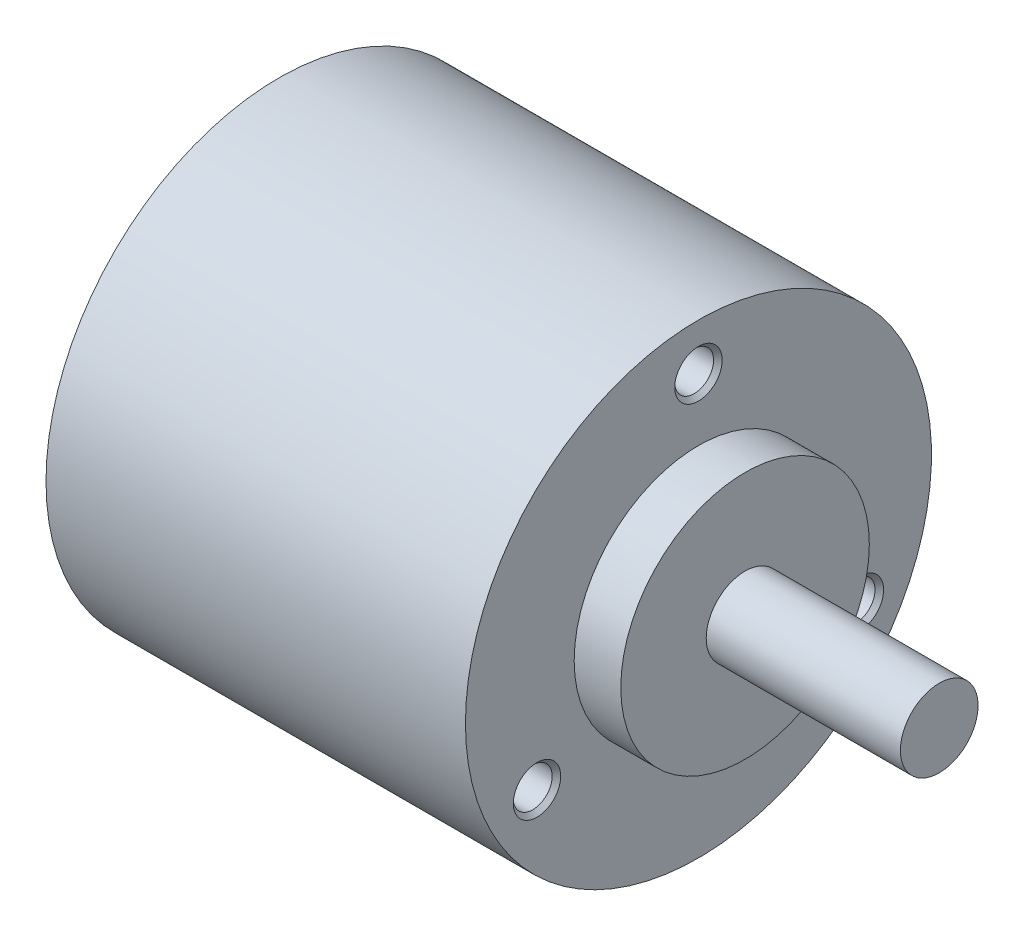
SolidWorks part; units mm, degrees
ref_plane "Plan de face" through (0, 0, 0) normal (0, 0, 1) x (1, 0, 0)
ref_plane "Plan de dessus" through (0, 0, 0) normal (0, 1, 0) x (1, 0, 0)
ref_plane "Plan de droite" through (0, 0, 0) normal (1, 0, 0) x (0, 0, -1)
sketch "Esquisse1" plane through (0, 0, 0) normal (0, 0, 1) x (1, 0, 0)
  line L0 (-51.1551, 0) -> (25.063, 0) construction
  line L1 (15.5, 2.5) -> (15.5, 0)
  line L2 (15.5, 0) -> (-27, 0)
  line L3 (-27, 0) -> (-27, 15)
  line L4 (-27, 15) -> (0, 15)
  line L5 (0, 15) -> (0, 8)
  line L6 (3, 2.5) -> (15.5, 2.5)
  line L7 (0, 8) -> (3, 8)
  line L8 (3, 8) -> (3, 2.5)
  dimension "D1" = 30
  dimension "D2" = 5
  dimension "D3" = 15.5
  dimension "D4" = 27
  dimension "D5" = 3
  dimension "D6" = 16
revolve "Révolution1" add sketch "Esquisse1" angle 360 about L0
hole_wizard "Trou taraudé M3x0.51" positions "Esquisse4" profile "Esquisse3" tap size "M3x0.5" standard "Ansi Metric"
sketch "Esquisse4" plane through (0, 0, 0) normal (1, 0, 0) x (0, 0, -1)
  circle A0 centre (0, 0) radius 12 construction
  point P0 (0, 12)
  point P2 (-10.3923, -6)
  point P8 (10.3923, -6)
  point P11 (0, 0)
  point P12 (0, -11)
  point P13 (-8.3544, -7.1557)
  dimension "D1" = 24
  dimension "D2" = 120
sketch "Esquisse3" plane through (0, 12, 0) normal (0, 1, 0) x (0, 0, -1)
  line L0 (0, 0) -> (0, 9.2511)
  line L1 (0, 9.2511) -> (1.25, 8.5)
  line L2 (1.25, 8.5) -> (1.25, 0.275)
  line L3 (1.25, 0.275) -> (1.525, 0)
  line L5 (1.525, 0) -> (0, 0)
  line L6 (-1.25, 0.275) -> (-1.525, 0) construction
  line L10 (0, 9.2511) -> (-1.25, 8.5) construction
  line L11 (0, -6.35) -> (0, 107.95) construction
  dimension "Diamètre du trou pour taraudage" = 2.5
  dimension "Profondeur du trou pour taraudage" = 8.5
  dimension "Diamètre du fraisage entrant" = 3.05
  dimension "Angle du fraisage entrant" = 90
  dimension "Angle de pointe" = 118
cosmetic thread "Filetage de perçage1" parameters "D1"=6, "D2"=3
cosmetic thread "Filetage de perçage2" parameters "D1"=6, "D2"=3
cosmetic thread "Filetage de perçage3" parameters "D1"=6, "D2"=3
